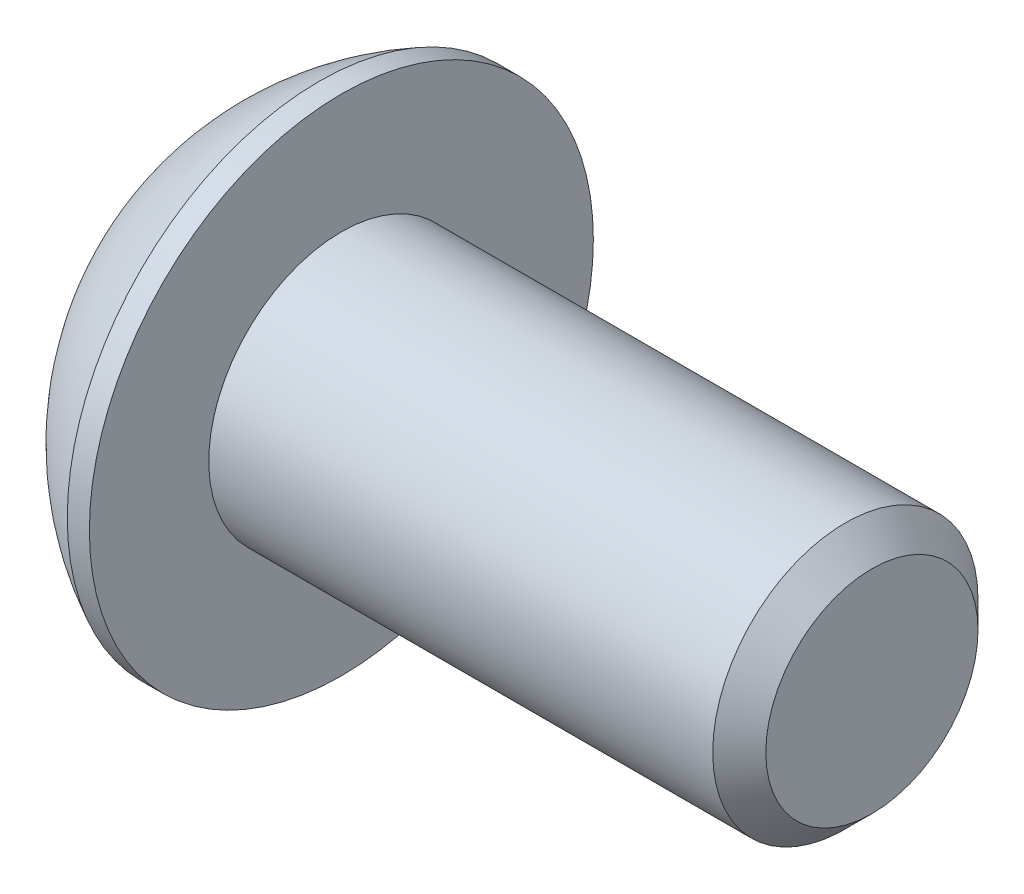
SolidWorks part; units mm, degrees
material "Plain Carbon Steel"
ref_plane "Front Plane" through (0, 0, 0) normal (0, 0, 1) x (1, 0, 0)
ref_plane "Top Plane" through (0, 0, 0) normal (0, 1, 0) x (1, 0, 0)
ref_plane "Right Plane" through (0, 0, 0) normal (1, 0, 0) x (0, 0, -1)
sketch "Sketch2" plane through (0, 0, 0) normal (1, 0, 0) x (0, 0, -1)
  circle A0 centre (0, 0) radius 1.5
  dimension "D1" = 3
extrude "Boss-Extrude1" add sketch "Sketch2" against normal blind 6
chamfer "Chamfer1" distance 0.3 angle 45 1 edges at (0, 0, -1.5)
sketch "Sketch6" plane through (0, 0, 0) normal (0, 0, 1) x (1, 0, 0)
  line L0 (-7.65, 0) -> (-7.65, 1.5)
  line L1 (-7.65, 0) -> (-6, 0)
  line L2 (-6.25, 2.85) -> (-6, 2.85)
  line L6 (-6, 2.85) -> (-6, 0)
  line L8 (-6, 0) -> (-14.6471, 0) construction
  line L10 (-6, 1.5) -> (-6, -1.5) construction
  arc A0 (-7.65, 1.5) -> (-6.25, 2.85) centre (-4.8527, 0) cw
  dimension "D3" = 0.25
  dimension "D1" = 5.7
  dimension "D2" = 1.65
  dimension "D4" = 3
revolve "Revolve1" add sketch "Sketch6" angle 360 about L8
sketch "Sketch7" plane through (-7.65, 0, 0) normal (-1, 0, 0) x (0, 0, 1)
  line L1 (0, 1.1547) -> (-1, 0.5774)
  line L2 (-1, 0.5774) -> (-1, -0.5774)
  line L3 (-1, -0.5774) -> (0, -1.1547)
  line L4 (0, -1.1547) -> (1, -0.5774)
  line L5 (1, -0.5774) -> (1, 0.5774)
  line L6 (1, 0.5774) -> (0, 1.1547)
  circle A0 centre (0, 0) radius 1 construction
  dimension "D1" = 2
extrude "Cut-Extrude1" cut sketch "Sketch7" against normal blind 1.2
sketch "Sketch8" plane through (-7.65, 0, 0) normal (-1, 0, 0) x (0, 0, 1)
  circle A0 centre (0, 0) radius 1.2047
  dimension "D1" = 0.05
extrude "Cut-Extrude2" cut sketch "Sketch8" against normal blind 1 draft 45
